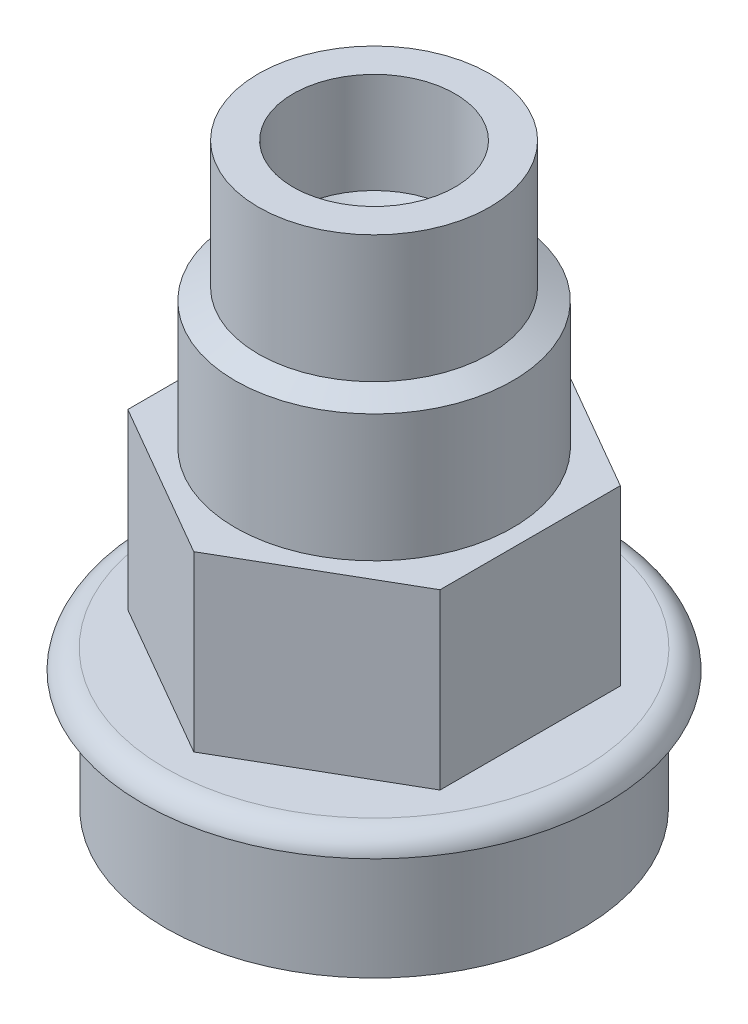
SolidWorks part; units mm, degrees
ref_plane "Front Plane" through (0, 0, 0) normal (0, 0, 1) x (1, 0, 0)
ref_plane "Top Plane" through (0, 0, 0) normal (0, 1, 0) x (1, 0, 0)
ref_plane "Right Plane" through (0, 0, 0) normal (1, 0, 0) x (0, 0, -1)
sketch "Sketch1" plane through (0, 0, 0) normal (1, 0, 0) x (0, 0, -1)
  line L0 (0, 25) -> (0, -25) construction
  line L3 (13, -24) -> (13, -13)
  line L4 (13, -13) -> (18.0292, -13)
  line L5 (20, -14.6595) -> (18, -14.6595)
  line L6 (18, -14.6595) -> (18, -25)
  line L7 (18, -25) -> (14.1517, -25)
  line L8 (14.1517, -25) -> (13, -24)
  line L9 (10, 25) -> (7, 25)
  line L10 (7, 25) -> (7, 16.3)
  line L11 (7, 16.3) -> (6, 15.3)
  line L12 (6, 15.3) -> (6, 10)
  line L13 (6, 10) -> (7, 10)
  line L14 (7, 10) -> (7, 2)
  line L15 (7, 2) -> (12, 2)
  line L16 (12, 2) -> (12, 13)
  line L17 (12, 13) -> (10, 14)
  line L18 (10, 14) -> (10, 25)
  arc A0 (18.0292, -13) -> (20, -14.6595) centre (18.0292, -15) cw
  point P3 (0, 0)
  point P17 (0, 0)
  point P21 (0, 0)
  point P22 (18.7393, 11.9223)
  dimension "D7" = 2
  dimension "D1" = 50
  dimension "D2" = 20
  dimension "D3" = 1
  dimension "D4" = 18
  dimension "D5" = 13
  dimension "D6" = 12
  dimension "D8" = 7
  dimension "D9" = 6
  dimension "D10" = 7
  dimension "D11" = 10
  dimension "D12" = 12
  dimension "D13" = 11
  dimension "D14" = 1
  dimension "D15" = 11
  dimension "D16" = 8
  dimension "D17" = 5.3
  dimension "D18" = 1
revolve "Revolve1" add sketch "Sketch1" angle 360 about L0
sketch "Sketch2" plane through (0, -13, 0) normal (0, 1, 0) x (1, 0, 0)
  line L1 (0, 15.5885) -> (-13.5, 7.7942)
  line L2 (-13.5, 7.7942) -> (-13.5, -7.7942)
  line L3 (-13.5, -7.7942) -> (0, -15.5885)
  line L4 (0, -15.5885) -> (13.5, -7.7942)
  line L5 (13.5, -7.7942) -> (13.5, 7.7942)
  line L6 (13.5, 7.7942) -> (0, 15.5885)
  circle A0 centre (0, 0) radius 13.5 construction
  circle A1 centre (0, 0) radius 9
  dimension "D2" = 18
  dimension "D1" = 27
extrude "Boss-Extrude2" add sketch "Sketch2" along normal up to surface (15 mm away) up to face at (0, 2, 12)
